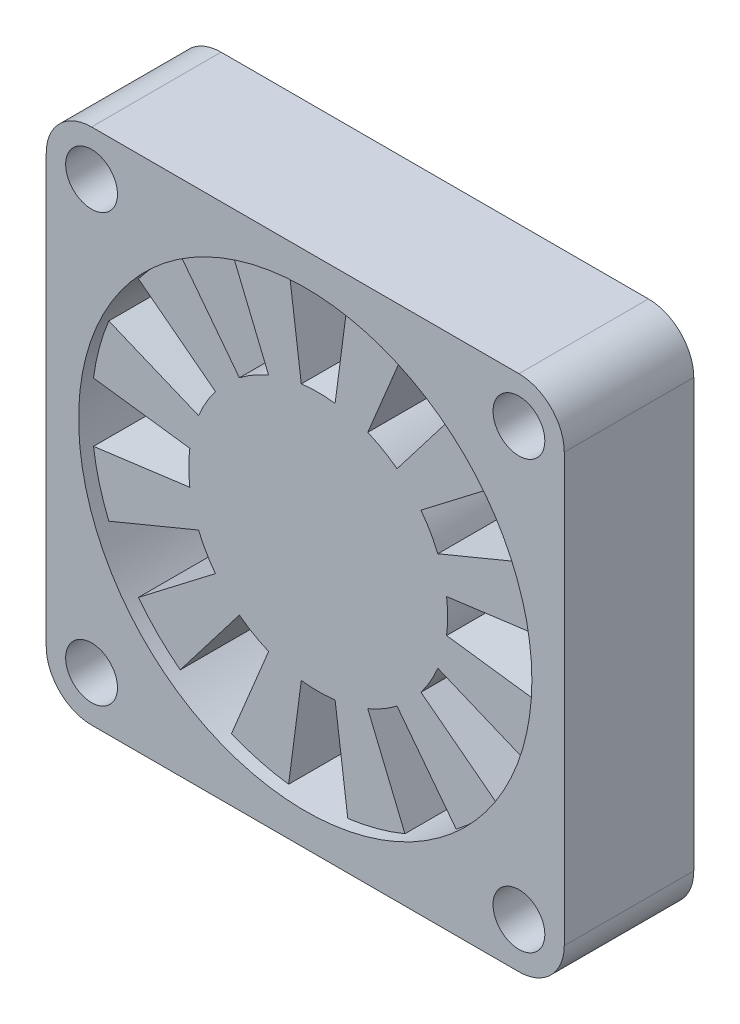
SolidWorks part; units mm, degrees
ref_plane "Front Plane" through (0, 0, 0) normal (0, 0, 1) x (1, 0, 0)
ref_plane "Top Plane" through (0, 0, 0) normal (0, 1, 0) x (1, 0, 0)
ref_plane "Right Plane" through (0, 0, 0) normal (1, 0, 0) x (0, 0, -1)
sketch "Sketch1" plane through (0, 0, 0) normal (0, 0, 1) x (1, 0, 0)
  line L1 (-20, -20) -> (20, -20)
  line L2 (-20, -20) -> (-20, 20)
  line L3 (-20, 20) -> (20, 20)
  line L4 (20, -20) -> (20, 20)
  line L5 (-20, -20) -> (20, 20) construction
  line L6 (-20, 20) -> (20, -20) construction
  point P0 (0, 0)
  dimension "D1" = 40
  dimension "D2" = 40
extrude "Boss-Extrude1" add sketch "Sketch1" along normal blind 10
fillet "Fillet1" radius 3.5 4 edges at (-20, 20, 5) (20, 20, 5) (-20, -20, 5) (20, -20, 5)
sketch "Sketch2" plane through (0, 0, 10) normal (0, 0, 1) x (1, 0, 0)
  line L1 (-16.5, -16.5) -> (16.5, -16.5) construction
  line L2 (-16.5, -16.5) -> (-16.5, 16.5) construction
  line L3 (-16.5, 16.5) -> (16.5, 16.5) construction
  line L4 (16.5, -16.5) -> (16.5, 16.5) construction
  line L5 (-16.5, -16.5) -> (16.5, 16.5) construction
  line L6 (-16.5, 16.5) -> (16.5, -16.5) construction
  circle A0 centre (16.5, -16.5) radius 2
  arc A1 (16.5, -20) -> (20, -16.5) centre (16.5, -16.5) ccw construction
  circle A2 centre (16.5, 16.5) radius 2
  circle A3 centre (-16.5, 16.5) radius 2
  circle A4 centre (-16.5, -16.5) radius 2
  point P2 (0, 0)
  dimension "D1" = 4
extrude "Cut-Extrude1" cut sketch "Sketch2" against normal through all
sketch "Sketch5" plane through (0, 0, 10) normal (0, 0, 1) x (1, 0, 0)
  line L0 (0, 0) -> (17.3503, 2.2842)
  line L1 (0, 0) -> (17.3503, -2.2842)
  line L2 (0, 0) -> (33.9191, 0) construction
  circle A0 centre (0, 0) radius 17.5
  circle A1 centre (0, 0) radius 10
  dimension "D1" = 20
  dimension "D2" = 35
  dimension "D3" = 15
extrude "Cut-Extrude2" cut sketch "Sketch5" against normal through all contours L2 A1 L1 A0 | A1 L2 A0 L0
pattern_circular "CirPattern1" count 12 over 360 about axis through (0, 0, 0) along (0, 0, 1) of "Cut-Extrude2"
sketch "Sketch6" plane through (0, 0, 10) normal (0, 0, 1) x (1, 0, 0)
  circle A0 centre (0, 0) radius 17.5
  dimension "D1" = 35
extrude "Cut-Extrude3" cut sketch "Sketch6" against normal blind 1
